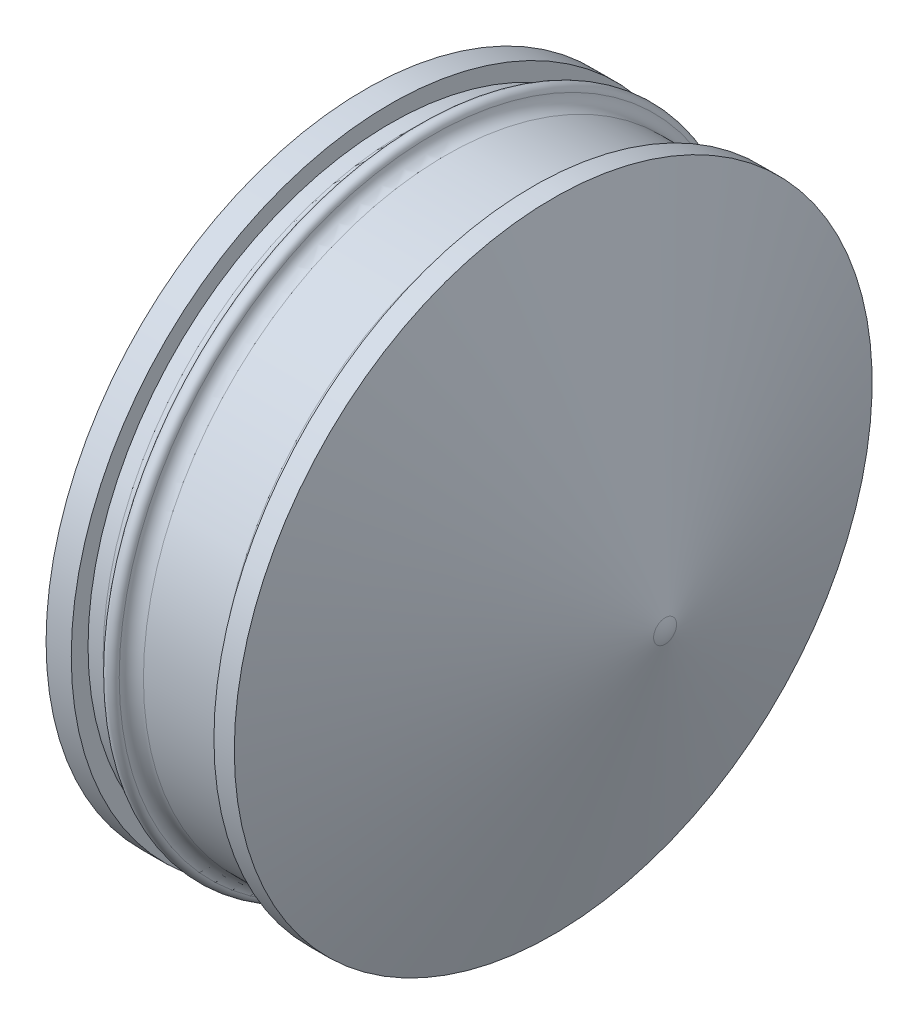
SolidWorks part; units mm, degrees
ref_plane "Front Plane" through (0, 0, 0) normal (0, 0, 1) x (1, 0, 0)
ref_plane "Top Plane" through (0, 0, 0) normal (0, 1, 0) x (1, 0, 0)
ref_plane "Right Plane" through (0, 0, 0) normal (1, 0, 0) x (0, 0, -1)
sketch "Sketch1" plane through (0, 0, 0) normal (0, 0, 1) x (1, 0, 0)
  line L0 (-0.6996, 0) -> (13.6888, 0) construction
  line L1 (4.3584, 0) -> (-4.3584, 0) construction
  line L2 (0, 12.065) -> (0.9525, 12.065)
  line L3 (0.9525, 12.065) -> (0.9525, 11.43)
  line L4 (3.048, 11.43) -> (5.842, 11.43)
  line L5 (6.35, 11.938) -> (6.35, 12.065)
  line L6 (6.35, 12.065) -> (7.1202, 12.065)
  line L7 (7.1202, 12.065) -> (11.3534, 0.4344)
  line L8 (0, 12.065) -> (0, 0)
  line L9 (0, -14.4873) -> (0, 14.4873) construction
  line L10 (0, 0) -> (11.43, 0)
  line L11 (2.286, 14.0596) -> (2.286, -1.1619) construction
  line L12 (0.9525, 11.43) -> (1.524, 11.43)
  arc A0 (11.3534, 0.4344) -> (11.43, 0) centre (10.16, 0) cw
  arc A1 (1.524, 11.43) -> (2.0237, 11.8464) centre (1.524, 11.938) ccw
  arc A2 (2.0237, 11.8464) -> (2.5483, 11.8464) centre (2.286, 11.7983) cw
  arc A3 (2.5483, 11.8464) -> (3.048, 11.43) centre (3.048, 11.938) ccw
  arc A4 (6.35, 11.938) -> (5.842, 11.43) centre (5.842, 11.938) cw
  dimension "D7" = 1.27
  dimension "D10" = 0.508
  dimension "D11" = 0.508
  dimension "D1" = 24.13
  dimension "D2" = 22.86
  dimension "D3" = 0.9525
  dimension "D4" = 6.35
  dimension "D5" = 70
  dimension "D6" = 11.43
  dimension "D8" = 2.286
  dimension "D9" = 1.524
revolve "Revolve: OD" add sketch "Sketch1" angle 360 about L0
sketch "Sketch3" plane through (0, 0, 0) normal (0, 0, 1) x (1, 0, 0)
  line L0 (0, 0) -> (0, 7.62)
  line L2 (0, 7.62) -> (2.0955, 7.62)
  line L3 (2.0955, 7.62) -> (2.0955, 11.303)
  line L4 (2.0955, 11.303) -> (5.7757, 11.303)
  line L5 (5.7757, 11.303) -> (9.8897, 0)
  line L7 (9.8897, 0) -> (0, 0)
  line L8 (0, -14.4873) -> (0, 14.4873) construction
  line L10 (11.3534, 0.4344) -> (7.1202, 12.065) construction
  line L11 (-1.4699, 0) -> (13.6442, 0) construction
  line L12 (4.3584, 0) -> (-4.3584, 0) construction
  dimension "D1" = 15.24
  dimension "D3" = 2.0955
  dimension "D4" = 22.606
  dimension "D5" = 1.524
revolve "Cut-Revolve: ID" cut sketch "Sketch3" angle 360 about L11
